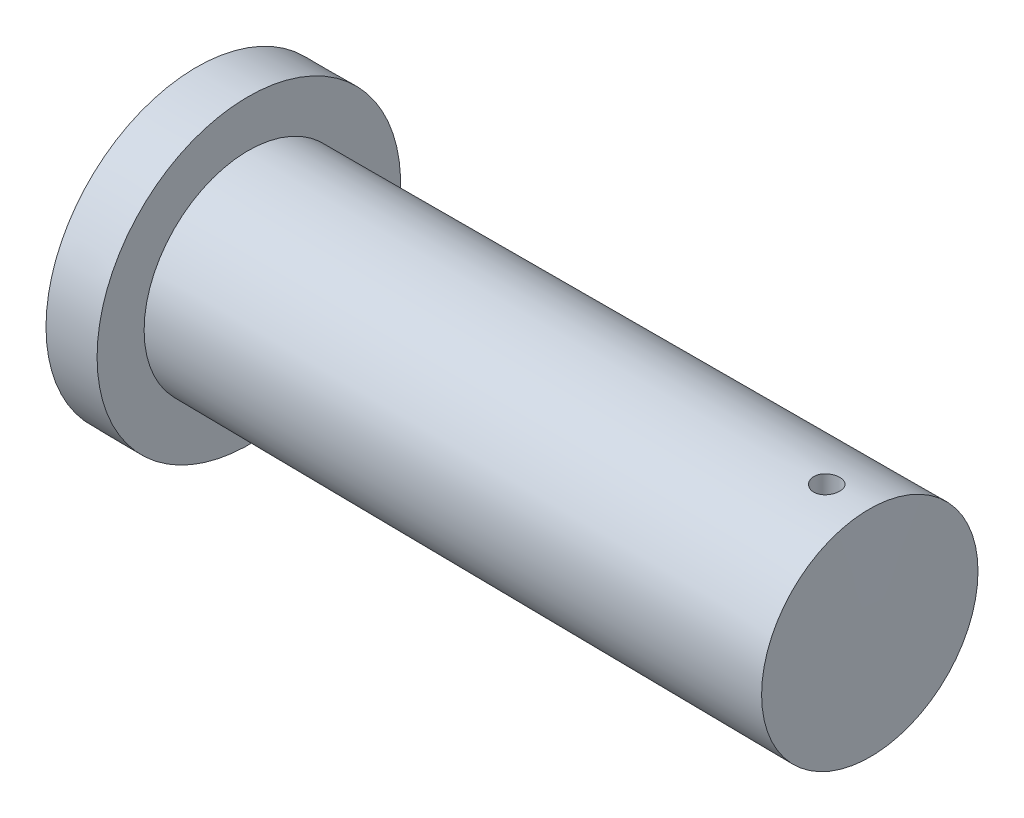
SolidWorks part; units mm, degrees
ref_plane "Front Plane" through (0, 0, 0) normal (0, 0, 1) x (1, 0, 0)
ref_plane "Top Plane" through (0, 0, 0) normal (0, 1, 0) x (1, 0, 0)
ref_plane "Right Plane" through (0, 0, 0) normal (1, 0, 0) x (0, 0, -1)
sketch "Sketch1" plane through (0, 0, 0) normal (0, 1, 0) x (1, 0, 0)
  line L0 (-420.9957, -76.2987) -> (1149.0043, -84.9567)
  line L1 (1149.0043, -84.9567) -> (1149.0043, 165.0433)
  line L2 (1149.0043, 165.0433) -> (-301.5949, 165.0433)
  line L3 (-301.5949, 165.0433) -> (-300.9957, 273.7013)
  line L4 (-300.9957, 273.7013) -> (-420.9957, 273.7013)
  line L5 (-420.9957, 273.7013) -> (-420.9957, -76.2987)
  dimension "D1" = 250
  dimension "D2" = 120
  dimension "D3" = 350
  dimension "D4" = 1570
revolve "Revolve1" add sketch "Sketch1" angle 360 about L0
sketch "Sketch3" plane through (0, 0, 0) normal (0, 1, 0) x (1, 0, 0)
  line L0 (-304.2639, -318.9429) -> (-301.5949, 165.0433) construction
  line L1 (1147.6257, -84.9491) -> (-302.9294, -76.9498) construction
  circle A0 centre (1047.0501, -84.3945) radius 30
  point P4 (0, 0)
  point P6 (1049.5971, -83.6176)
  dimension "D1" = 60
  dimension "D2" = 1350
extrude "Cut-Extrude1" cut sketch "Sketch3" against normal through all both and the other way through all
